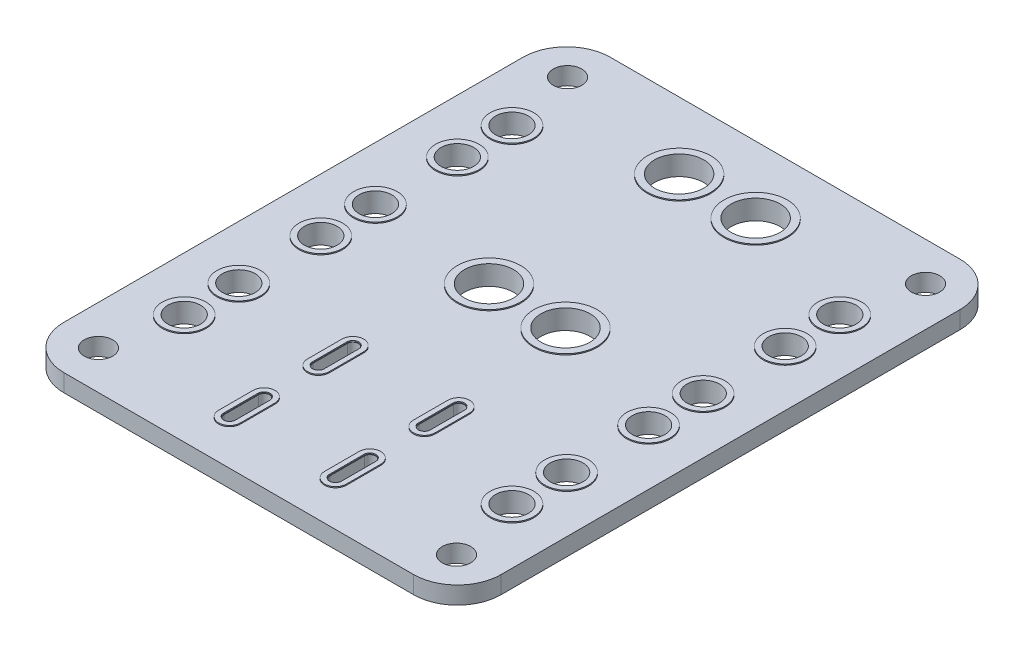
SolidWorks part; units mm, degrees
ref_plane "Alzado" through (0, 0, 0) normal (0, 0, 1) x (1, 0, 0)
ref_plane "Planta" through (0, 0, 0) normal (0, 1, 0) x (1, 0, 0)
ref_plane "Vista lateral" through (0, 0, 0) normal (1, 0, 0) x (0, 0, -1)
sketch "Croquis1" plane through (0, 0, 0) normal (0, 1, 0) x (1, 0, 0)
  line L1 (-16, 25) -> (16, 25)
  line L2 (-20, 21) -> (-20, -21)
  line L3 (-16, -25) -> (16, -25)
  line L4 (20, 21) -> (20, -21)
  line L5 (-20, 25) -> (20, -25) construction
  line L6 (-20, -25) -> (20, 25) construction
  arc A0 (16, 25) -> (20, 21) centre (16, 21) cw
  arc A1 (16, -25) -> (20, -21) centre (16, -21) ccw
  arc A2 (-20, -21) -> (-16, -25) centre (-16, -21) ccw
  arc A3 (-16, 25) -> (-20, 21) centre (-16, 21) ccw
  point P0 (0, 0)
  dimension "D1" = 4
  dimension "D2" = 50
  dimension "D3" = 40
extrude "Saliente-Extruir1" add sketch "Croquis1" along normal mid plane 1.6
sketch "Croquis2" plane through (0, 0.8, 0) normal (0, 1, 0) x (1, 0, 0)
  line L1 (16.383, -21.463) -> (-16.383, -21.463) construction
  line L2 (16.383, -21.463) -> (16.383, 21.463) construction
  line L3 (16.383, 21.463) -> (-16.383, 21.463) construction
  line L4 (-16.383, -21.463) -> (-16.383, 21.463) construction
  line L5 (16.383, -21.463) -> (-16.383, 21.463) construction
  line L6 (16.383, 21.463) -> (-16.383, -21.463) construction
  circle A0 centre (-16.383, 21.463) radius 1.3
  circle A1 centre (16.383, 21.463) radius 1.3
  circle A2 centre (16.383, -21.463) radius 1.3
  circle A3 centre (-16.383, -21.463) radius 1.3
  point P0 (0, 0)
  dimension "D1" = 2.6
  dimension "D2" = 21.463
  dimension "D3" = 16.383
extrude "Cortar-Extruir1" cut sketch "Croquis2" against normal through all both and the other way through all
sketch "Croquis6" plane through (0, 0.8, 0) normal (0, 1, 0) x (1, 0, 0)
  line L0 (-3.5, 18.796) -> (3.5, 18.796) construction
  line L1 (0, 23.1314) -> (0, -25.294) construction
  line L2 (-15, 15) -> (-15, 10) construction
  line L3 (-15, 2.5) -> (-15, -2.5) construction
  line L4 (-15, -10) -> (-15, -15) construction
  line L8 (-3.5, -15.36) -> (3.5, -15.36) construction
  line L9 (-5.7074, 10.0965) -> (6.7794, 10.0965) construction
  line L10 (4.847, -9.721) -> (4.847, -12.871) construction
  line L11 (5.347, -9.721) -> (5.347, -12.871)
  line L12 (4.347, -9.721) -> (4.347, -12.871)
  line L13 (-4.847, -9.721) -> (-4.847, -12.871) construction
  line L14 (-5.347, -9.721) -> (-5.347, -12.871)
  line L15 (-4.347, -9.721) -> (-4.347, -12.871)
  line L16 (4.847, -20.999) -> (4.847, -17.849) construction
  line L17 (5.347, -20.999) -> (5.347, -17.849)
  line L18 (4.347, -20.999) -> (4.347, -17.849)
  line L19 (-4.847, -20.999) -> (-4.847, -17.849) construction
  line L20 (-5.347, -20.999) -> (-5.347, -17.849)
  line L21 (-4.347, -20.999) -> (-4.347, -17.849)
  line L22 (-3.5, 1.397) -> (3.5, 1.397) construction
  line L23 (4.847, -11.296) -> (4.847, -19.424) construction
  circle A0 centre (-3.5, 18.796) radius 2.25
  circle A1 centre (3.5, 18.796) radius 2.25
  circle A2 centre (-15, 2.5) radius 1.5
  circle A3 centre (-15, -2.5) radius 1.5
  circle A4 centre (-15, 10) radius 1.5
  circle A5 centre (-15, 15) radius 1.5
  circle A6 centre (-15, -10) radius 1.5
  circle A7 centre (-15, -15) radius 1.5
  circle A8 centre (15, -15) radius 1.5
  circle A9 centre (15, -10) radius 1.5
  circle A10 centre (15, 15) radius 1.5
  circle A11 centre (15, 10) radius 1.5
  circle A12 centre (15, -2.5) radius 1.5
  circle A13 centre (15, 2.5) radius 1.5
  arc A16 (5.347, -9.721) -> (4.347, -9.721) centre (4.847, -9.721) ccw
  arc A17 (4.347, -12.871) -> (5.347, -12.871) centre (4.847, -12.871) ccw
  arc A18 (-5.347, -9.721) -> (-4.347, -9.721) centre (-4.847, -9.721) cw
  arc A19 (-4.347, -12.871) -> (-5.347, -12.871) centre (-4.847, -12.871) cw
  arc A20 (5.347, -20.999) -> (4.347, -20.999) centre (4.847, -20.999) cw
  arc A21 (4.347, -17.849) -> (5.347, -17.849) centre (4.847, -17.849) cw
  arc A22 (-5.347, -20.999) -> (-4.347, -20.999) centre (-4.847, -20.999) ccw
  arc A23 (-4.347, -17.849) -> (-5.347, -17.849) centre (-4.847, -17.849) ccw
  circle A24 centre (3.5, 1.397) radius 2.25
  circle A25 centre (-3.5, 1.397) radius 2.25
  point P4 (0, 18.796)
  point P32 (-15, 0)
  point P33 (-15, 12.5)
  point P34 (-15, -12.5)
  point P46 (4.847, -11.296)
  point P54 (-4.847, -11.296)
  point P61 (4.847, -19.424)
  point P68 (-4.847, -19.424)
  point P73 (4.847, -15.36)
  dimension "D1" = 3
  dimension "D8" = 4.5
  dimension "D2" = 5
  dimension "D3" = 5
  dimension "D4" = 5
  dimension "D5" = 15
  dimension "D6" = 12.5
  dimension "D7" = 12.5
  dimension "D9" = 7
  dimension "D10" = 18.796
  dimension "D11" = 1
  dimension "D12" = 3.15
  dimension "D13" = 1.397
  dimension "D14" = 4.847
  dimension "D15" = 15.36
  dimension "D16" = 8.128
extrude "Cortar-Extruir3" cut sketch "Croquis6" against normal through all
sketch "Croquis7" plane through (0, 0, 0) normal (0, 1, 0) x (1, 0, 0)
  line L0 (0, 6.6749) -> (0, -3.6027) construction
  line L8 (-4.297, -12.871) -> (-4.297, -9.721)
  line L9 (-5.397, -9.721) -> (-5.397, -12.871)
  line L10 (-4.297, -12.871) -> (-4.297, -9.721)
  line L11 (-5.397, -9.721) -> (-5.397, -12.871)
  line L13 (5.397, -12.871) -> (5.397, -9.721)
  line L14 (4.297, -9.721) -> (4.297, -12.871)
  line L15 (5.397, -12.871) -> (5.397, -9.721)
  line L16 (4.297, -9.721) -> (4.297, -12.871)
  line L22 (-4.297, -20.999) -> (-4.297, -17.849)
  line L23 (-5.397, -17.849) -> (-5.397, -20.999)
  line L24 (-4.297, -20.999) -> (-4.297, -17.849)
  line L25 (-5.397, -17.849) -> (-5.397, -20.999)
  line L31 (5.397, -20.999) -> (5.397, -17.849)
  line L32 (4.297, -17.849) -> (4.297, -20.999)
  line L33 (5.397, -20.999) -> (5.397, -17.849)
  line L34 (-3.847, -12.871) -> (-3.847, -9.721)
  line L35 (-5.847, -9.721) -> (-5.847, -12.871)
  line L36 (-3.847, -12.871) -> (-3.847, -9.721)
  line L37 (-5.847, -9.721) -> (-5.847, -12.871)
  line L38 (4.297, -17.849) -> (4.297, -20.999)
  line L44 (5.847, -12.871) -> (5.847, -9.721)
  line L45 (3.847, -9.721) -> (3.847, -12.871)
  line L46 (5.847, -12.871) -> (5.847, -9.721)
  line L47 (3.847, -9.721) -> (3.847, -12.871)
  line L54 (-5.847, -17.849) -> (-5.847, -20.999)
  line L55 (-3.847, -20.999) -> (-3.847, -17.849)
  line L56 (-5.847, -17.849) -> (-5.847, -20.999)
  line L57 (-3.847, -20.999) -> (-3.847, -17.849)
  line L64 (5.847, -20.999) -> (5.847, -17.849)
  line L65 (3.847, -17.849) -> (3.847, -20.999)
  line L66 (5.847, -20.999) -> (5.847, -17.849)
  line L67 (3.847, -17.849) -> (3.847, -20.999)
  circle A0 centre (-15, -15) radius 1.5
  circle A1 centre (-15, -10) radius 1.5
  circle A2 centre (-15, -2.5) radius 1.5
  circle A3 centre (-15, 2.5) radius 1.5
  circle A4 centre (-15, 10) radius 1.5
  circle A5 centre (-15, 15) radius 1.5
  circle A6 centre (-15, 15) radius 1.5 construction
  circle A7 centre (-15, 15) radius 2
  circle A8 centre (-15, 10) radius 2
  circle A9 centre (-15, 2.5) radius 2
  circle A10 centre (-15, -2.5) radius 2
  circle A11 centre (-15, -15) radius 2
  circle A12 centre (-15, -10) radius 2
  circle A13 centre (-3.5, 18.796) radius 2.25
  circle A14 centre (-3.5, 18.796) radius 2.8949
  circle A15 centre (3.5, 18.796) radius 2.8949
  circle A16 centre (3.5, 18.796) radius 2.25
  circle A17 centre (15, -10) radius 2
  circle A18 centre (15, -15) radius 2
  circle A19 centre (15, -2.5) radius 2
  circle A20 centre (15, 2.5) radius 2
  circle A21 centre (15, 10) radius 2
  circle A22 centre (15, 15) radius 2
  circle A23 centre (15, 15) radius 1.5
  circle A24 centre (15, 10) radius 1.5
  circle A25 centre (15, 2.5) radius 1.5
  circle A26 centre (15, -2.5) radius 1.5
  circle A27 centre (15, -10) radius 1.5
  circle A28 centre (15, -15) radius 1.5
  circle A29 centre (3.5, 1.397) radius 2.25
  circle A30 centre (3.5, 1.397) radius 2.8949
  circle A31 centre (-3.5, 1.397) radius 2.8949
  circle A32 centre (-3.5, 1.397) radius 2.25
  arc A39 (-5.397, -12.871) -> (-4.297, -12.871) centre (-4.847, -12.871) ccw
  arc A40 (-4.297, -9.721) -> (-5.397, -9.721) centre (-4.847, -9.721) ccw
  arc A41 (-5.397, -12.871) -> (-4.297, -12.871) centre (-4.847, -12.871) ccw
  arc A42 (-4.297, -9.721) -> (-5.397, -9.721) centre (-4.847, -9.721) ccw
  arc A43 (4.297, -12.871) -> (5.397, -12.871) centre (4.847, -12.871) ccw
  arc A44 (5.397, -9.721) -> (4.297, -9.721) centre (4.847, -9.721) ccw
  arc A45 (4.297, -12.871) -> (5.397, -12.871) centre (4.847, -12.871) ccw
  arc A46 (5.397, -9.721) -> (4.297, -9.721) centre (4.847, -9.721) ccw
  arc A52 (-5.397, -20.999) -> (-4.297, -20.999) centre (-4.847, -20.999) ccw
  arc A53 (-4.297, -17.849) -> (-5.397, -17.849) centre (-4.847, -17.849) ccw
  arc A54 (-5.397, -20.999) -> (-4.297, -20.999) centre (-4.847, -20.999) ccw
  arc A55 (-4.297, -17.849) -> (-5.397, -17.849) centre (-4.847, -17.849) ccw
  arc A61 (4.297, -20.999) -> (5.397, -20.999) centre (4.847, -20.999) ccw
  arc A62 (5.397, -17.849) -> (4.297, -17.849) centre (4.847, -17.849) ccw
  arc A63 (4.297, -20.999) -> (5.397, -20.999) centre (4.847, -20.999) ccw
  arc A64 (5.397, -17.849) -> (4.297, -17.849) centre (4.847, -17.849) ccw
  arc A67 (-5.847, -12.871) -> (-3.847, -12.871) centre (-4.847, -12.871) ccw
  arc A68 (-3.847, -9.721) -> (-5.847, -9.721) centre (-4.847, -9.721) ccw
  arc A69 (-5.847, -12.871) -> (-3.847, -12.871) centre (-4.847, -12.871) ccw
  arc A70 (-3.847, -9.721) -> (-5.847, -9.721) centre (-4.847, -9.721) ccw
  arc A75 (3.847, -12.871) -> (5.847, -12.871) centre (4.847, -12.871) ccw
  arc A76 (5.847, -9.721) -> (3.847, -9.721) centre (4.847, -9.721) ccw
  arc A77 (3.847, -12.871) -> (5.847, -12.871) centre (4.847, -12.871) ccw
  arc A78 (5.847, -9.721) -> (3.847, -9.721) centre (4.847, -9.721) ccw
  arc A83 (-5.847, -20.999) -> (-3.847, -20.999) centre (-4.847, -20.999) ccw
  arc A84 (-3.847, -17.849) -> (-5.847, -17.849) centre (-4.847, -17.849) ccw
  arc A85 (-5.847, -20.999) -> (-3.847, -20.999) centre (-4.847, -20.999) ccw
  arc A86 (-3.847, -17.849) -> (-5.847, -17.849) centre (-4.847, -17.849) ccw
  arc A91 (5.847, -17.849) -> (3.847, -17.849) centre (4.847, -17.849) ccw
  arc A92 (3.847, -20.999) -> (5.847, -20.999) centre (4.847, -20.999) ccw
  arc A93 (5.847, -17.849) -> (3.847, -17.849) centre (4.847, -17.849) ccw
  arc A94 (3.847, -20.999) -> (5.847, -20.999) centre (4.847, -20.999) ccw
  dimension "D1" = 4
  dimension "D2" = 0.5
  dimension "D3" = 0.5
  dimension "D4" = 0.5
  dimension "D5" = 0.5
  dimension "D6" = 0.05
  dimension "D7" = 0.05
  dimension "D8" = 0.05
  dimension "D9" = 0.05
extrude "Saliente-Extruir3" add sketch "Croquis7" along normal mid plane 1.8
